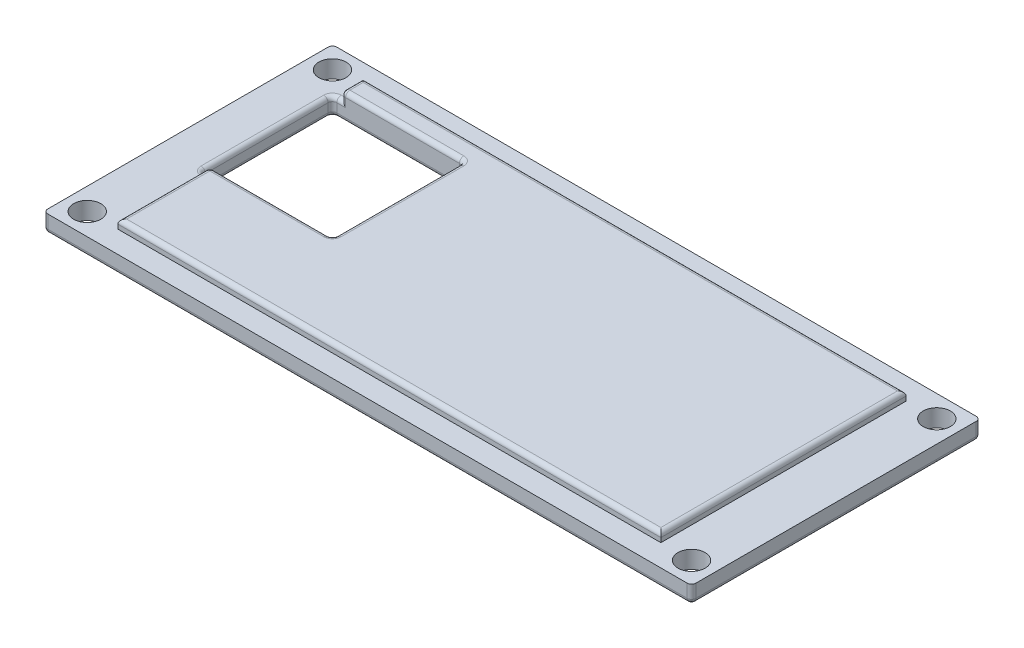
SolidWorks part; units mm, degrees
ref_plane "Front Plane" through (0, 0, 0) normal (0, 0, 1) x (1, 0, 0)
ref_plane "Top Plane" through (0, 0, 0) normal (0, 1, 0) x (1, 0, 0)
ref_plane "Right Plane" through (0, 0, 0) normal (1, 0, 0) x (0, 0, -1)
sketch "Sketch1" plane through (0, 0, 0) normal (0, 1, 0) x (1, 0, 0)
  line L1 (0, 0) -> (74, 0)
  line L2 (0, 0) -> (0, 33)
  line L3 (0, 33) -> (74, 33)
  line L4 (74, 0) -> (74, 33)
  dimension "D1" = 33
  dimension "D2" = 74
extrude "Boss-Extrude1" add sketch "Sketch1" along normal blind 2
sketch "Sketch2" plane through (0, 2, 0) normal (0, 1, 0) x (1, 0, 0)
  line L0 (0, 33) -> (0, 0) construction
  line L1 (6, 30.5) -> (68, 30.5)
  line L2 (6, 30.5) -> (6, 2.5)
  line L3 (6, 2.5) -> (68, 2.5)
  line L4 (68, 30.5) -> (68, 2.5)
  line L5 (74, 0) -> (74, 33) construction
  line L6 (0, 0) -> (74, 0) construction
  line L7 (74, 33) -> (0, 33) construction
  dimension "D1" = 6
  dimension "D2" = 6
  dimension "D3" = 2.5
  dimension "D4" = 2.5
extrude "Boss-Extrude2" add sketch "Sketch2" along normal blind 1
sketch "Sketch3" plane through (0, 2, 0) normal (0, 1, 0) x (1, 0, 0)
  line L0 (0, 33) -> (0, 0) construction
  line L1 (74, 33) -> (0, 33) construction
  line L2 (0, 0) -> (74, 0) construction
  line L3 (74, 0) -> (74, 33) construction
  circle A0 centre (2.5, 30.5) radius 1.55
  circle A1 centre (71.5, 2.5) radius 1.55
  circle A2 centre (2.5, 2.5) radius 1.55
  circle A3 centre (71.5, 30.5) radius 1.55
  dimension "D1" = 3.1
  dimension "D2" = 2.5
  dimension "D3" = 2.5
  dimension "D4" = 3.1
  dimension "D5" = 2.5
  dimension "D6" = 2.5
  dimension "D7" = 3.1
  dimension "D8" = 2.5
  dimension "D9" = 2.5
  dimension "D10" = 3.1
  dimension "D11" = 2.5
  dimension "D12" = 2.5
extrude "Cut-Extrude2" cut sketch "Sketch3" against normal blind 5
fillet "Fillet1" radius 0.5 4 edges at (37, 3, -30.5) (68, 3, -16.5) (37, 3, -2.5) (6, 3, -16.5)
fillet "Fillet2" radius 0.5 8 edges at (37, 0, 0) (74, 0, -16.5) (37, 0, -33) (0, 0, -16.5) (74, 1, 0) (74, 1, -33) (0, 1, -33) (0, 1, 0)
sketch "Sketch4" plane through (0, 0, 0) normal (0, -1, 0) x (1, 0, 0)
  line L0 (73.5, -33) -> (0.5, -33) construction
  line L1 (5, -28) -> (20, -28)
  line L2 (5, -28) -> (5, -13)
  line L3 (5, -13) -> (20, -13)
  line L4 (20, -28) -> (20, -13)
  line L5 (0, -32.5) -> (0, -0.5) construction
  dimension "D1" = 5
  dimension "D2" = 5
  dimension "D3" = 15
  dimension "D4" = 15
extrude "Cut-Extrude3" cut sketch "Sketch4" against normal blind 10
fillet "Fillet3" radius 0.5 18 edges at (20, 0, -20.5) (20, 3, -20.5) (5.5, 2, -28) (6, 2.25, -28) (6.1464, 2.8536, -28) (13.25, 3, -28) (20, 1.5, -28) (12.5, 0, -28) (5, 2, -20.5) (5, 1, -28) (5, 0, -20.5) (5.5, 2, -13) (5, 1, -13) (12.5, 0, -13) (20, 1.5, -13) (13.25, 3, -13) (6.1464, 2.8536, -13) (6, 2.25, -13)
